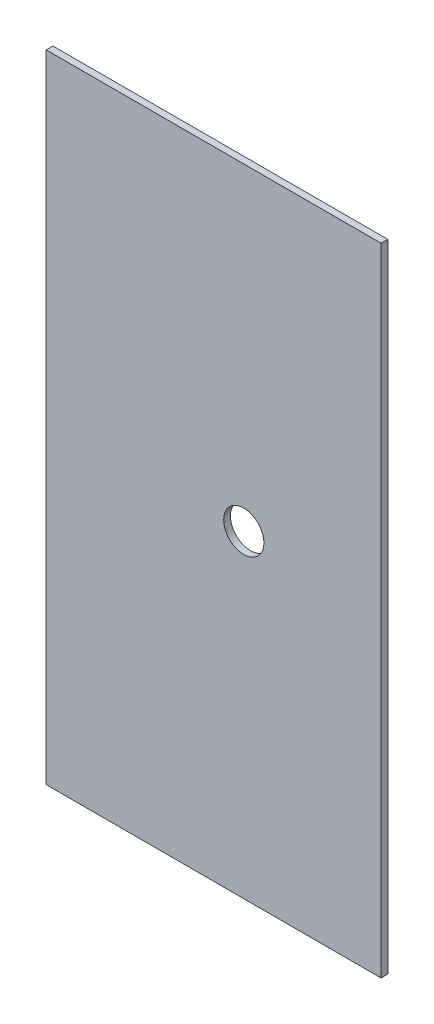
SolidWorks part; units mm, degrees
ref_plane "Front Plane" through (0, 0, 0) normal (0, 0, 1) x (1, 0, 0)
ref_plane "Top Plane" through (0, 0, 0) normal (0, 1, 0) x (1, 0, 0)
ref_plane "Right Plane" through (0, 0, 0) normal (1, 0, 0) x (0, 0, -1)
sketch "Sketch1" plane through (0, 0, 0) normal (0, 0, 1) x (1, 0, 0)
  line L1 (-50, -95) -> (50, -95)
  line L2 (-50, -95) -> (-50, 95)
  line L3 (-50, 95) -> (50, 95)
  line L4 (50, -95) -> (50, 95)
  line L5 (-50, -95) -> (50, 95) construction
  line L6 (-50, 95) -> (50, -95) construction
  point P0 (0, 0)
  dimension "D1" = 190
  dimension "D2" = 100
extrude "Boss-Extrude1" add sketch "Sketch1" along normal blind 2
sketch "Sketch2" plane through (0, 0, 0) normal (0, 0, -1) x (-1, 0, 0)
  circle A0 centre (-9, 0) radius 6
  dimension "D1" = 12
extrude "Cut-Extrude1" cut sketch "Sketch2" against normal blind 2
